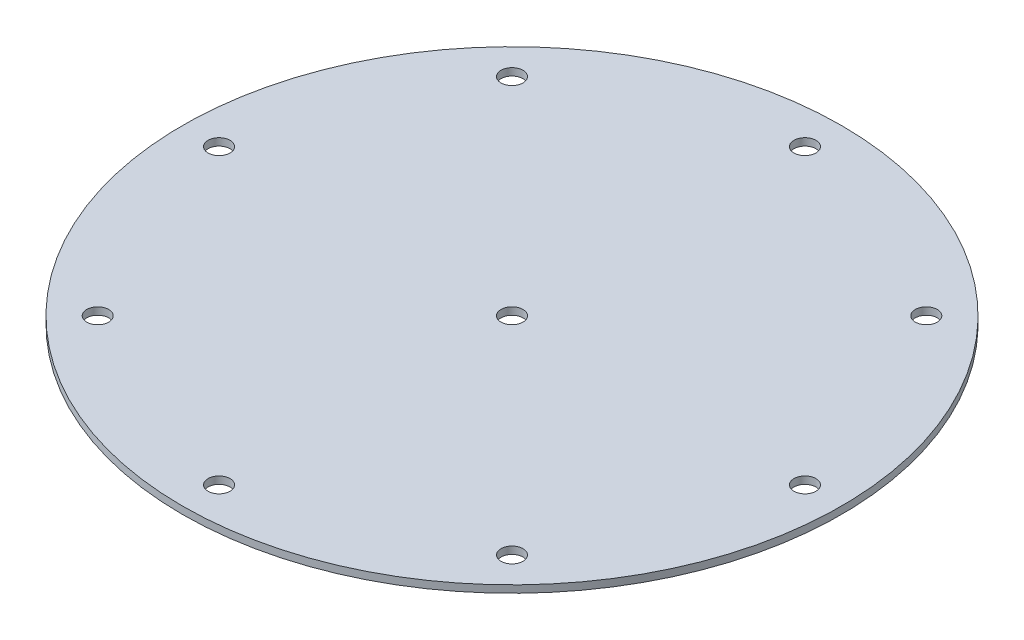
SolidWorks part; units mm, degrees
ref_plane "Front Plane" through (0, 0, 0) normal (0, 0, 1) x (1, 0, 0)
ref_plane "Top Plane" through (0, 0, 0) normal (0, 1, 0) x (1, 0, 0)
ref_plane "Right Plane" through (0, 0, 0) normal (1, 0, 0) x (0, 0, -1)
sketch "Sketch1" plane through (0, 0, 0) normal (0, 1, 0) x (1, 0, 0)
  line L0 (0, 0) -> (0, 80) construction
  circle A0 centre (0, 0) radius 90
  circle A1 centre (0, 0) radius 3
  circle A2 centre (0, 80) radius 3
  circle A3 centre (56.5685, 56.5685) radius 3
  circle A4 centre (80, 0) radius 3
  circle A5 centre (56.5685, -56.5685) radius 3
  circle A6 centre (0, -80) radius 3
  circle A7 centre (-56.5685, -56.5685) radius 3
  circle A8 centre (-80, 0) radius 3
  circle A9 centre (-56.5685, 56.5685) radius 3
  dimension "D1" = 180
  dimension "D2" = 6
  dimension "D3" = 6
  dimension "D4" = 80
  dimension "D6" = 80
  dimension "D5" = 8
extrude "Boss-Extrude1" add sketch "Sketch1" along normal blind 2
